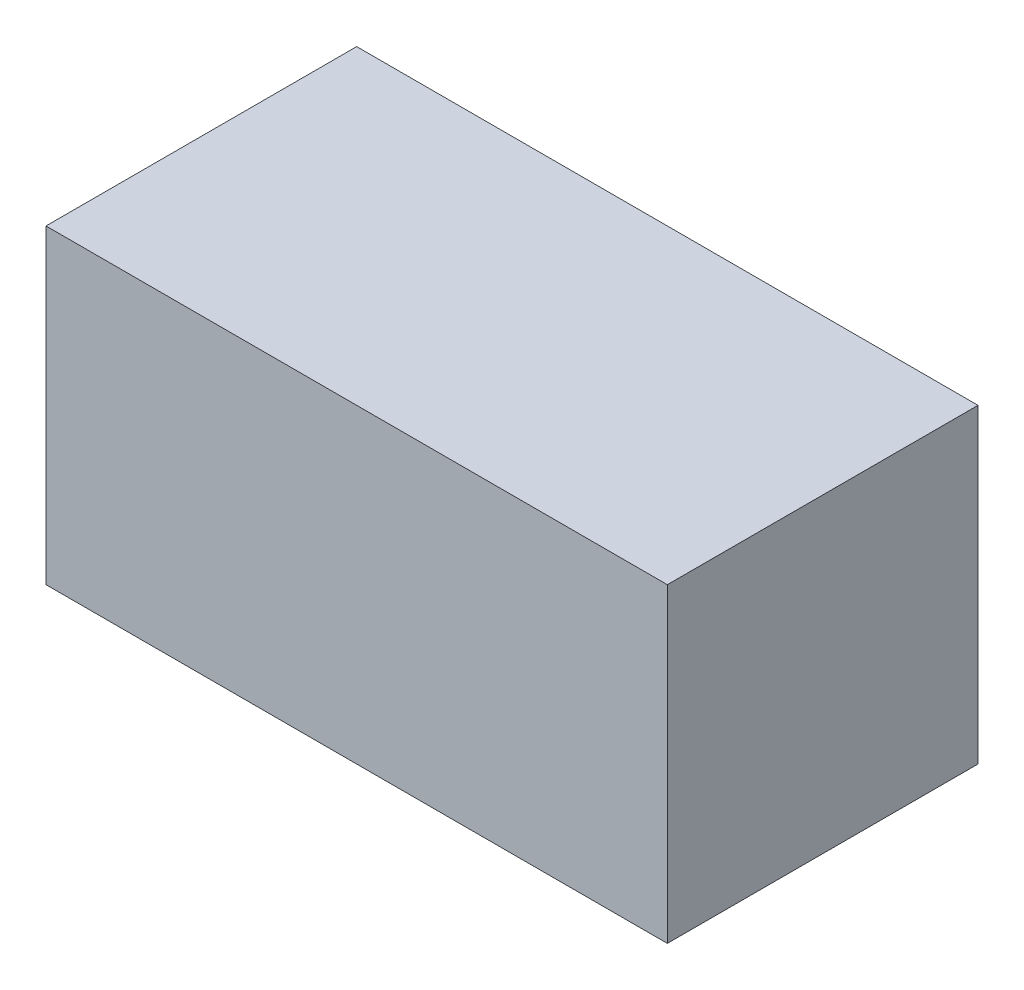
SolidWorks part; units mm, degrees
ref_plane "Front Plane" through (0, 0, 0) normal (0, 0, 1) x (1, 0, 0)
ref_plane "Top Plane" through (0, 0, 0) normal (0, 1, 0) x (1, 0, 0)
ref_plane "Right Plane" through (0, 0, 0) normal (1, 0, 0) x (0, 0, -1)
sketch "Sketch1" plane through (0, 0, 0) normal (0, 0, 1) x (1, 0, 0)
  line L1 (-1, -0.5) -> (1, -0.5)
  line L2 (-1, -0.5) -> (-1, 0.5)
  line L3 (-1, 0.5) -> (1, 0.5)
  line L4 (1, -0.5) -> (1, 0.5)
  line L5 (-1, -0.5) -> (1, 0.5) construction
  line L6 (-1, 0.5) -> (1, -0.5) construction
  point P0 (0, 0)
  dimension "D1" = 2
  dimension "D2" = 1
extrude "Boss-Extrude1" add sketch "Sketch1" along normal blind 1
